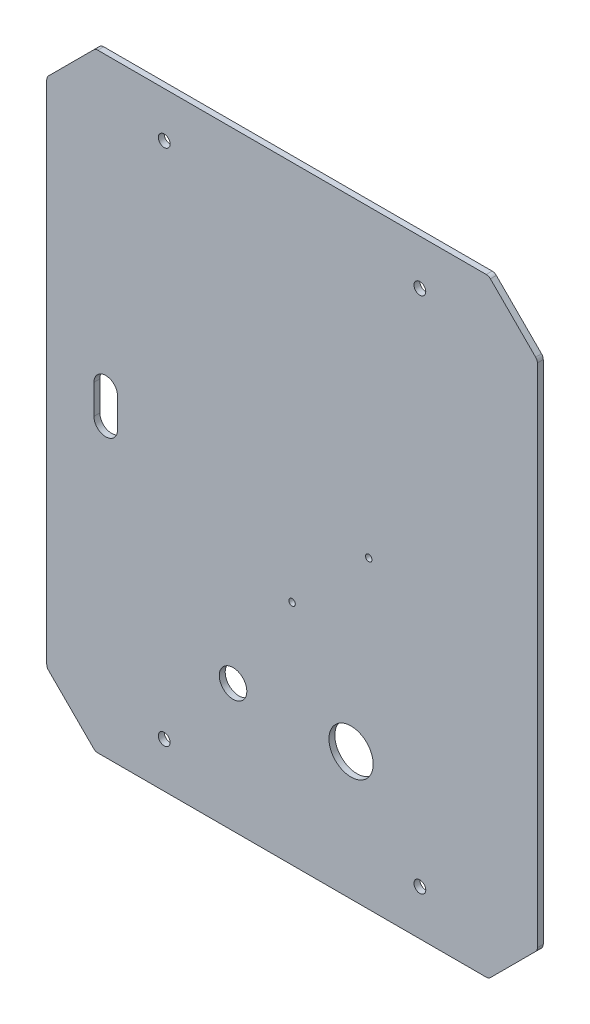
SolidWorks part; units mm, degrees
material "Verre"
ref_plane "Plan de dessus" through (0, 0, 0) normal (0, 0, 1) x (1, 0, 0)
ref_plane "Plan de droite" through (0, 0, 0) normal (0, 1, 0) x (1, 0, 0)
ref_plane "Plan de face" through (0, 0, 0) normal (1, 0, 0) x (0, 0, -1)
sketch "Esquisse1" plane through (0, 0, 0) normal (0, 0, 1) x (1, 0, 0)
  line L0 (0, 0) -> (-200, 0)
  line L1 (-200, 0) -> (-224.7487, 24.7487)
  line L2 (-224.7487, 24.7487) -> (-224.7487, 284.7487)
  line L3 (-224.7487, 284.7487) -> (-200, 309.4975)
  line L4 (-200, 309.4975) -> (0, 309.4975)
  line L5 (0, 309.4975) -> (24.7487, 284.7487)
  line L6 (24.7487, 284.7487) -> (24.7487, 24.7487)
  line L7 (24.7487, 24.7487) -> (0, 0)
  dimension "D1" = 260
  dimension "D2" = 35
  dimension "D3" = 135
  dimension "D4" = 200
extrude "Base" add sketch "Esquisse1" along normal blind 3
fillet "Congé1" radius 3 8 edges at (-200, 0, 1.5) (-224.7487, 24.7487, 1.5) (-224.7487, 284.7487, 1.5) (-200, 309.4975, 1.5) (0, 309.4975, 1.5) (24.7487, 284.7487, 1.5) (24.7487, 24.7487, 1.5) (0, 0, 1.5)
sketch "Esquisse19" plane through (0, 0, 0) normal (0, 0, -1) x (-1, 0, 0)
  line L0 (100, 309.4975) -> (100, 0) construction
  line L1 (1.2426, 309.4975) -> (198.7574, 309.4975) construction
  line L2 (198.7574, 0) -> (1.2426, 0) construction
  line L3 (-24.7487, 154.7487) -> (224.7487, 154.7487) construction
  line L4 (-24.7487, 25.9914) -> (-24.7487, 283.5061) construction
  line L5 (224.7487, 283.5061) -> (224.7487, 25.9914) construction
sketch "Esquisse20" plane through (0, 0, 0) normal (0, 0, -1) x (-1, 0, 0)
  line L0 (35, 286.4975) -> (35, 309.4975) construction
  line L1 (1.2426, 309.4975) -> (198.7574, 309.4975) construction
  line L2 (35, 286.4975) -> (100, 286.4975) construction
  line L3 (100, 309.4975) -> (100, 0) construction
  line L4 (100, 309.4975) -> (100, 0) construction
  line L5 (198.7574, 0) -> (1.2426, 0) construction
  line L6 (-24.7487, 154.7487) -> (224.7487, 154.7487) construction
  line L7 (-24.7487, 25.9914) -> (-24.7487, 283.5061) construction
  circle A0 centre (35, 286.4975) radius 3
  circle A1 centre (165, 286.4975) radius 3
  circle A2 centre (165, 23) radius 3
  circle A3 centre (35, 23) radius 3
  dimension "D3" = 6
  dimension "D1" = 65
  dimension "D2" = 23
extrude "Perçage Profilés" cut sketch "Esquisse20" against normal through all
sketch "Esquisse21" plane through (0, 0, 0) normal (0, 0, -1) x (-1, 0, 0)
  line L1 (100, 154.7487) -> (100, 115.7487) construction
  line L2 (100, 309.4975) -> (100, 0) construction
  line L3 (100, 154.7487) -> (61, 154.7487) construction
  line L4 (-24.7487, 154.7487) -> (224.7487, 154.7487) construction
  circle A1 centre (61, 154.7487) radius 1.65
  circle A2 centre (100, 115.7487) radius 1.65
  dimension "D2" = 3.3
  dimension "D1" = 39
extrude "Perçage Lidar" cut sketch "Esquisse21" against normal through all
sketch "Esquisse22" plane through (0, 0, 0) normal (0, 0, -1) x (-1, 0, 0)
  line L0 (100, 309.4975) -> (100, 0) construction
  line L1 (198.7574, 0) -> (1.2426, 0) construction
  circle A0 centre (70, 65) radius 11.25
  dimension "D1" = 22.5
  dimension "D2" = 30
  dimension "D3" = 65
extrude "Perçage Arret d'urgence" cut sketch "Esquisse22" against normal through all
sketch "Esquisse23" plane through (0, 0, 0) normal (0, 0, -1) x (-1, 0, 0)
  line L0 (198.7574, 0) -> (1.2426, 0) construction
  line L1 (100, 309.4975) -> (100, 0) construction
  circle A0 centre (130, 65) radius 7
  dimension "D1" = 14
  dimension "D2" = 65
  dimension "D3" = 30
extrude "Perçage Tirette" cut sketch "Esquisse23" against normal through all
sketch "Esquisse24" plane through (0, 0, 0) normal (0, 0, -1) x (-1, 0, 0)
  line L0 (194.7487, 147.2487) -> (194.7487, 162.2487) construction
  line L1 (188.7487, 147.2487) -> (188.7487, 162.2487)
  line L2 (200.7487, 147.2487) -> (200.7487, 162.2487)
  line L3 (-24.7487, 154.7487) -> (224.7487, 154.7487) construction
  line L4 (224.7487, 283.5061) -> (224.7487, 25.9914) construction
  arc A0 (188.7487, 147.2487) -> (200.7487, 147.2487) centre (194.7487, 147.2487) ccw
  arc A1 (200.7487, 162.2487) -> (188.7487, 162.2487) centre (194.7487, 162.2487) ccw
  point P2 (194.7487, 154.7487)
  dimension "D1" = 6
  dimension "D2" = 15
  dimension "D3" = 30
extrude "Perçage Cable management" cut sketch "Esquisse24" against normal through all
